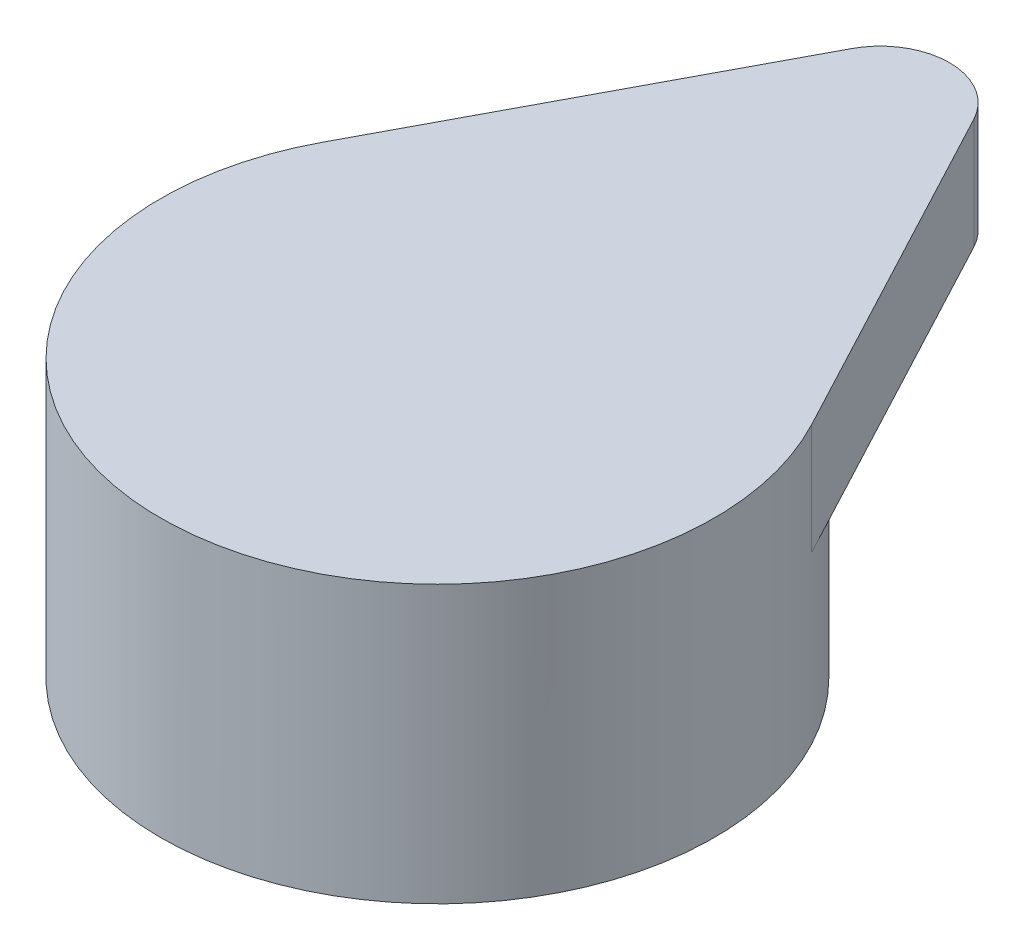
SolidWorks part; units mm, degrees
ref_plane "Front Plane" through (0, 0, 0) normal (0, 0, 1) x (1, 0, 0)
ref_plane "Top Plane" through (0, 0, 0) normal (0, 1, 0) x (1, 0, 0)
ref_plane "Right Plane" through (0, 0, 0) normal (1, 0, 0) x (0, 0, -1)
sketch "Sketch1" plane through (0, 0, 0) normal (0, 1, 0) x (1, 0, 0)
  circle A0 centre (0, 0) radius 5
  circle A1 centre (0, 0) radius 3
  dimension "D1" = 10
  dimension "D2" = 6
extrude "Boss-Extrude1" add sketch "Sketch1" along normal blind 3
sketch "Sketch2" plane through (0, 3, 0) normal (0, 1, 0) x (1, 0, 0)
  line L0 (0, 0) -> (0, 8) construction
  line L1 (-1.1042, 8.5859) -> (-4.4167, 2.3438)
  line L2 (4.4167, 2.3438) -> (1.1042, 8.5859)
  circle A0 centre (0, 8) radius 1.25
  circle A1 centre (0, 0) radius 5 construction
  circle A2 centre (0, 0) radius 5
  dimension "D2" = 2.5
  dimension "11mm" = 8
extrude "Boss-Extrude2" add sketch "Sketch2" along normal blind 2
